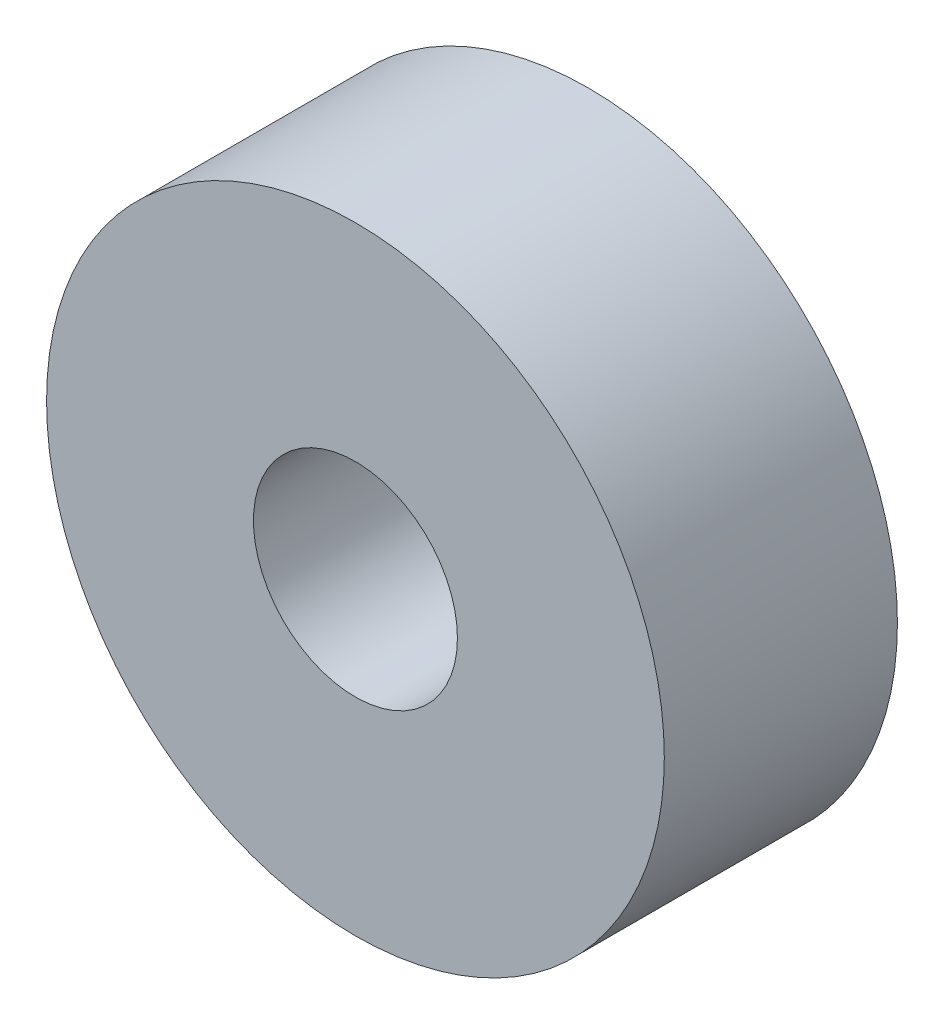
SolidWorks part; units mm, degrees
material "Резина"
ref_plane "Спереди" through (0, 0, 0) normal (0, 0, 1) x (1, 0, 0)
ref_plane "Сверху" through (0, 0, 0) normal (0, 1, 0) x (1, 0, 0)
ref_plane "Справа" through (0, 0, 0) normal (1, 0, 0) x (0, 0, -1)
sketch "Эскиз1" plane through (0, 0, 0) normal (0, 0, 1) x (1, 0, 0)
  circle A0 centre (0, 0) radius 35
  circle A1 centre (0, 0) radius 106
  dimension "D1" = 70
  dimension "D2" = 212
extrude "Бобышка-Вытянуть1" add sketch "Эскиз1" along normal blind 80
